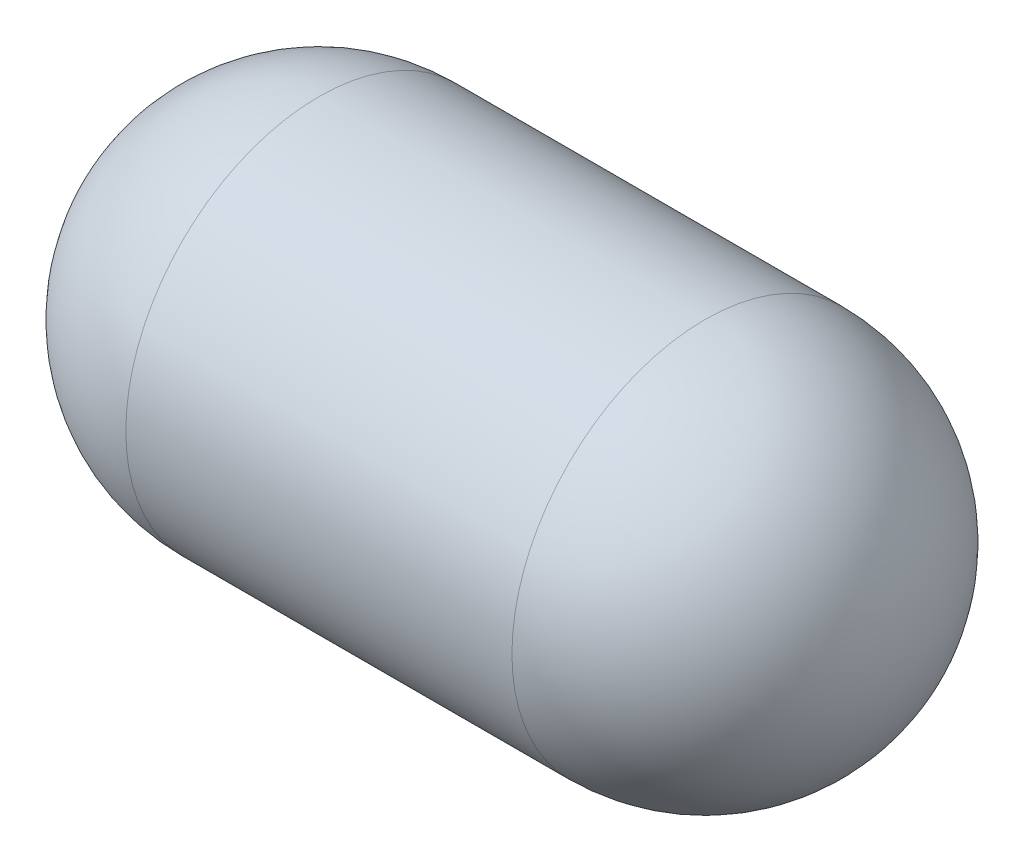
SolidWorks part; units mm, degrees
material "ABS"
ref_plane "Front Plane" through (0, 0, 0) normal (0, 0, 1) x (1, 0, 0)
ref_plane "Top Plane" through (0, 0, 0) normal (0, 1, 0) x (1, 0, 0)
ref_plane "Right Plane" through (0, 0, 0) normal (1, 0, 0) x (0, 0, -1)
sketch "Sketch1" plane through (0, 0, 0) normal (1, 0, 0) x (0, 0, -1)
  circle A0 centre (0, 0) radius 3.175
  dimension "D1" = 6.35
extrude "Boss-Extrude1" add sketch "Sketch1" along normal blind 12.7
fillet "Fillet1" radius 3.175 2 edges at (0, 0, -3.175) (12.7, 0, -3.175)
